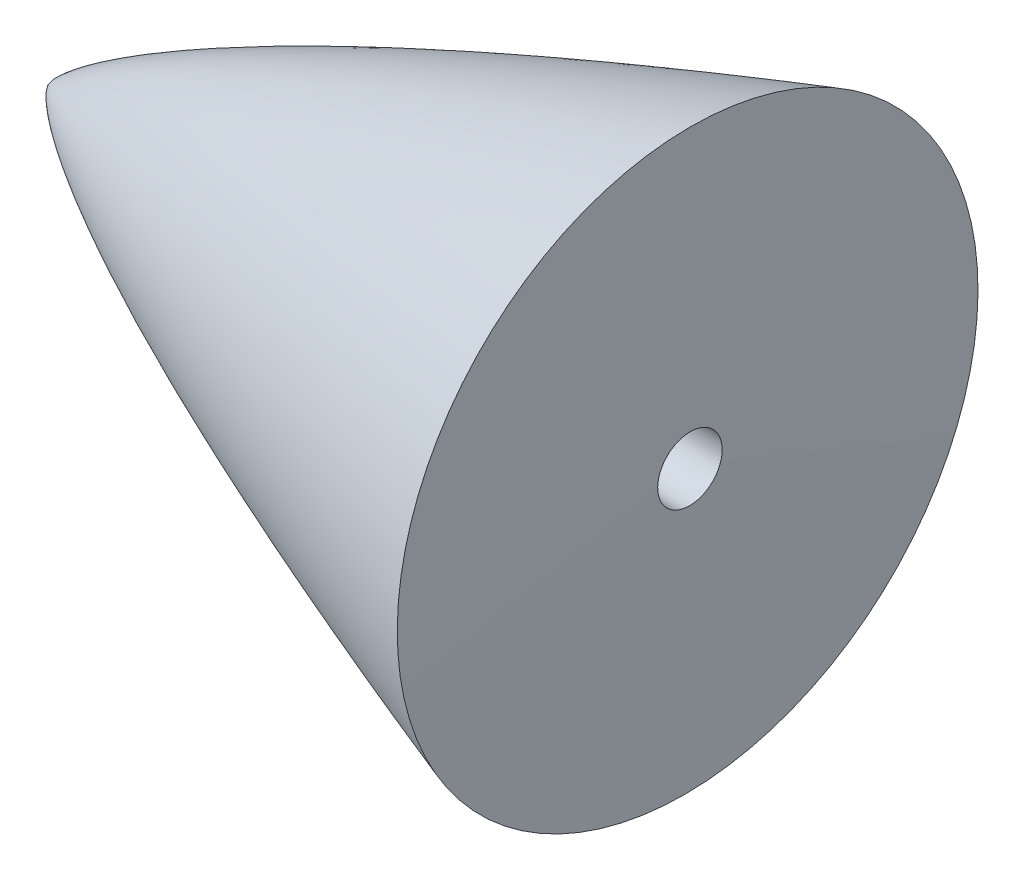
SolidWorks part; units mm, degrees
ref_plane "Front Plane" through (0, 0, 0) normal (0, 0, 1) x (1, 0, 0)
ref_plane "Top Plane" through (0, 0, 0) normal (0, 1, 0) x (1, 0, 0)
ref_plane "Right Plane" through (0, 0, 0) normal (1, 0, 0) x (0, 0, -1)
sketch "Sketch1" plane through (0, 0, 0) normal (0, 0, 1) x (1, 0, 0)
  line L0 (0, 0) -> (50.8, -0.4644)
  line L1 (50.8, -0.4644) -> (50.8, 22.5304)
  spline S0 degree 4 poles (0, 0) (0.0034, 0.018) (0.0111, 0.0443) (0.0276, 0.0824) (0.0564, 0.1398) (0.0969, 0.2096) (0.165, 0.3125) (0.2783, 0.4621) (0.4613, 0.6747) (0.7551, 0.9759) (1.2208, 1.3985) (1.948, 1.9843) (3.0376, 2.7663) (4.6883, 3.8283) (7.0687, 5.2032) (10.0936, 6.7823) (13.6413, 8.4827) (17.4617, 10.1905) (21.314, 11.8194) (25.1956, 13.386) (28.6053, 14.7087) (31.5467, 15.8166) (33.9916, 16.7185) (35.9736, 17.4379) (37.9137, 18.1333) (39.9342, 18.8455) (42.317, 19.6776) (44.945, 20.576) (47.1774, 21.3311) (50.1657, 22.3229) (51.8907, 22.8893) (54.2047, 23.6424) (55.1287, 23.9372) (55.9178, 24.1913) knots 0 0 0 0 0 0.00119 0.001793 0.002702 0.004188 0.006457 0.009843 0.01494 0.022485 0.033904 0.050863 0.075851 0.109982 0.161962 0.230225 0.298488 0.366751 0.435014 0.503277 0.57154 0.605671 0.639803 0.673934 0.708066 0.742197 0.776328 0.844591 0.878723 0.912854 0.956427 1 1 1 1 1 construction
  spline S1 degree 4 poles (0, 0) (0.0034, 0.018) (0.0111, 0.0443) (0.0276, 0.0824) (0.0564, 0.1398) (0.0969, 0.2096) (0.165, 0.3125) (0.2783, 0.4621) (0.4613, 0.6747) (0.7551, 0.9759) (1.2208, 1.3985) (1.948, 1.9843) (3.0376, 2.7663) (4.6883, 3.8283) (7.0687, 5.2032) (10.0936, 6.7823) (13.6413, 8.4827) (17.4617, 10.1905) (21.314, 11.8194) (25.1956, 13.386) (28.6053, 14.7087) (31.5467, 15.8166) (33.9916, 16.7185) (35.9736, 17.4379) (37.9137, 18.1333) (39.9342, 18.8455) (42.317, 19.6776) (44.945, 20.576) (47.1774, 21.3311) (49.4427, 22.0829) (50.3465, 22.3813) (50.8, 22.5304) knots 0 0 0 0 0 0.00119 0.001793 0.002702 0.004188 0.006457 0.009843 0.01494 0.022485 0.033904 0.050863 0.075851 0.109982 0.161962 0.230225 0.298488 0.366751 0.435014 0.503277 0.57154 0.605671 0.639803 0.673934 0.708066 0.742197 0.776328 0.844591 0.878723 0.912854 0.912854 0.912854 0.912854 0.912854
  dimension "D1" = 50.8
  dimension "D2" = 22.9948
revolve "Revolve3" add sketch "Sketch1" angle 360 about L0
ref_plane "Plane1" through (50.7915, -0.9288, 0) normal (0.9998, -0.0183, 0) x (0, 0, -1)
sketch "Sketch3" plane through (50.7915, -0.9288, 0) normal (0.9998, -0.0183, 0) x (0, 0, -1)
  line L0 (-24.6013, 0) -> (21.3252, 0) construction
  line L1 (0, -23.733) -> (0, 23.9549) construction
hole_wizard "1/4-20 Tapped Hole2" positions "3DSketch4" profile "Sketch5" tap size "1/4-20" standard "ANSI Inch"
sketch3d "3DSketch4"
  line L0 (50.7915, -0.9288, 24.6013) -> (50.7915, -0.9288, -21.3252) construction
  point P0 (50.7915, -0.9288, 0)
sketch "Sketch5" plane through (50.7915, -0.9288, 0) normal (0.0129, 0.707, 0.707) x (0.0129, 0.7069, -0.7072)
  line L0 (0, 0) -> (0, 26.9338)
  line L1 (0, 26.9338) -> (2.5527, 25.4)
  line L2 (2.5527, 25.4) -> (2.5527, 0)
  line L5 (2.5527, 0) -> (0, 0)
  line L10 (0, 26.9338) -> (-2.5527, 25.4) construction
  line L11 (0, -6.35) -> (0, 107.95) construction
  dimension "Tap Drill Dia." = 5.1054
  dimension "Tap Drill Depth" = 25.4
  dimension "Drill Angle" = 118
cosmetic thread "Hole Thread1" parameters "D1"=12.7, "D2"=6.35
